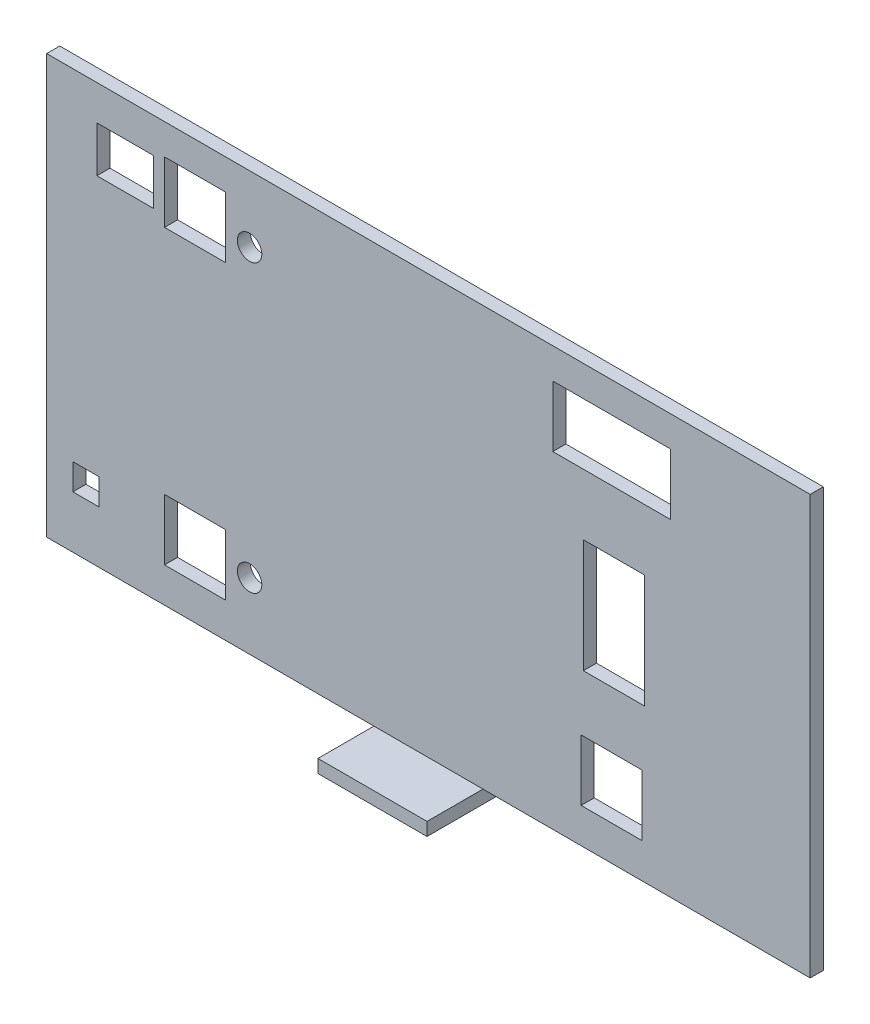
SolidWorks part; units mm, degrees
other "Markup1"
sketch "Sketch6" plane through (-87.5, -48, 0) normal (0, 0, -1) x (-1, 0, 0)
ref_plane "Front Plane" through (0, 0, 0) normal (0, 0, 1) x (1, 0, 0)
ref_plane "Top Plane" through (0, 0, 0) normal (0, 1, 0) x (1, 0, 0)
ref_plane "Right Plane" through (0, 0, 0) normal (1, 0, 0) x (0, 0, -1)
sketch "Sketch2" plane through (0, 0, 0) normal (0, 0, 1) x (1, 0, 0)
  line L1 (87.5, 48) -> (-87.5, 48)
  line L2 (87.5, 48) -> (87.5, -48)
  line L3 (87.5, -48) -> (-87.5, -48)
  line L4 (-87.5, 48) -> (-87.5, -48)
  line L5 (87.5, 48) -> (-87.5, -48) construction
  line L6 (87.5, -48) -> (-87.5, 48) construction
  point P0 (0, 0)
  dimension "D1" = 175
  dimension "D2" = 96
extrude "Boss-Extrude1" add sketch "Sketch2" along normal blind 3
sketch "Sketch3" plane through (0, 0, 0) normal (0, 0, -1) x (-1, 0, 0)
  line L0 (-87.5, 40) -> (-54.5, 40) construction
  line L1 (-87.5, -48) -> (-87.5, 48) construction
  line L2 (-87.5, 48) -> (87.5, 48) construction
  line L3 (-87.5, 28) -> (-29.5, 28) construction
  line L4 (-54.5, 40) -> (-42.5, 40)
  line L5 (-54.5, 40) -> (-54.5, 28)
  line L6 (-54.5, 28) -> (-42.5, 28)
  line L7 (-42.5, 40) -> (-42.5, 28)
  line L8 (87.5, 40) -> (59.5, 40) construction
  line L9 (-29.5, 28) -> (-41.5, 28)
  line L10 (-29.5, 28) -> (-29.5, 40)
  line L11 (-29.5, 40) -> (-41.5, 40)
  line L12 (-41.5, 28) -> (-41.5, 40)
  line L13 (87.5, 48) -> (87.5, -48) construction
  line L15 (59.5, 40) -> (47.5, 40)
  line L16 (59.5, 40) -> (59.5, 28)
  line L17 (59.5, 28) -> (47.5, 28)
  line L18 (47.5, 40) -> (47.5, 28)
  line L19 (63, 40) -> (76, 40)
  line L20 (63, 40) -> (63, 29.5)
  line L21 (63, 29.5) -> (76, 29.5)
  line L22 (76, 40) -> (76, 29.5)
  line L23 (-55.5, 41) -> (-28.5, 41)
  line L24 (-55.5, 41) -> (-55.5, 27)
  line L25 (-55.5, 27) -> (-28.5, 27)
  line L26 (-28.5, 41) -> (-28.5, 27)
  dimension "D1" = 33
  dimension "D2" = 8
  dimension "D3" = 12
  dimension "D4" = 12
  dimension "D5" = 58
  dimension "D6" = 12
  dimension "D7" = 12
  dimension "D8" = 28
  dimension "D9" = 12
  dimension "D10" = 12
  dimension "D11" = 11.5
  dimension "D12" = 13
  dimension "D13" = 10.5
  dimension "D14" = 1
  dimension "D15" = 1
  dimension "D16" = 1
  dimension "D17" = 1
extrude "Cut-Extrude1" cut sketch "Sketch3" against normal blind 10
sketch "Sketch4" plane through (0, 0, 0) normal (0, 0, -1) x (-1, 0, 0)
  line L0 (-87.5, 0) -> (-49.5, 0) construction
  line L1 (-87.5, -48) -> (-87.5, 48) construction
  line L2 (87.5, -48) -> (-87.5, -48) construction
  line L3 (-49.5, 13) -> (-35.5, 13)
  line L4 (-49.5, 13) -> (-49.5, -13)
  line L5 (-49.5, -13) -> (-35.5, -13)
  line L6 (-35.5, 13) -> (-35.5, -13)
  line L7 (-87.5, 48) -> (87.5, 48) construction
  dimension "D1" = 38
  dimension "D2" = 14
  dimension "D3" = 35
  dimension "D4" = 35
  dimension "D5" = 0
extrude "Cut-Extrude2" cut sketch "Sketch4" against normal blind 10
sketch "Sketch5" plane through (0, 0, 0) normal (0, 0, -1) x (-1, 0, 0)
  line L0 (-87.5, -39) -> (-48, -39) construction
  line L1 (-87.5, -48) -> (-87.5, 48) construction
  line L2 (87.5, -48) -> (-87.5, -48) construction
  line L3 (87.5, -39) -> (59.5, -39) construction
  line L4 (-48, -39) -> (-36, -39)
  line L5 (-48, -39) -> (-48, -27)
  line L6 (-48, -27) -> (-36, -27)
  line L7 (-36, -39) -> (-36, -27)
  line L8 (87.5, 48) -> (87.5, -48) construction
  line L9 (87.5, -36) -> (81.5, -36) construction
  line L10 (59.5, -39) -> (47.5, -39)
  line L11 (59.5, -39) -> (59.5, -27)
  line L12 (59.5, -27) -> (47.5, -27)
  line L13 (47.5, -39) -> (47.5, -27)
  line L15 (81.5, -36) -> (75.5, -36)
  line L16 (81.5, -36) -> (81.5, -30)
  line L17 (81.5, -30) -> (75.5, -30)
  line L18 (75.5, -36) -> (75.5, -30)
  dimension "D1" = 39.5
  dimension "D2" = 9
  dimension "D3" = 12
  dimension "D4" = 12
  dimension "D5" = 28
  dimension "D6" = 12
  dimension "D7" = 12
  dimension "D8" = 12
  dimension "D9" = 6
  dimension "D10" = 6
  dimension "D11" = 6
extrude "Cut-Extrude3" cut sketch "Sketch5" against normal blind 10
sketch "Sketch7" plane through (0, 0, 0) normal (0, 0, -1) x (-1, 0, 0)
  line L0 (41, 48) -> (41, 32.8) construction
  line L1 (-87.5, 48) -> (87.5, 48) construction
  line L2 (87.5, 48) -> (87.5, -48) construction
  line L3 (0, 0) -> (87.5, 0) construction
  circle A0 centre (41, 32.8) radius 2.8
  circle A1 centre (41, -32.8) radius 2.8
  dimension "D3" = 5.6
  dimension "D1" = 15.2
  dimension "D2" = 46.5
extrude "Cut-Extrude4" cut sketch "Sketch7" against normal blind 10
sketch "Sketch9" plane through (0, -48, 0) normal (0, -1, 0) x (1, 0, 0)
  line L0 (-87.5, 0) -> (87.5, 0) construction
  line L1 (12.5, 0) -> (-12.5, 0)
  line L2 (12.5, 0) -> (12.5, 15.8299)
  line L3 (12.5, 15.8299) -> (-12.5, 15.8299)
  line L4 (-12.5, 0) -> (-12.5, 15.8299)
  line L5 (-87.5, 3) -> (-87.5, 0) construction
  line L6 (87.5, 3) -> (87.5, 0) construction
  dimension "D1" = 75
  dimension "D2" = 75
extrude "Boss-Extrude2" add sketch "Sketch9" along normal blind 3
sketch "Sketch10" plane through (0, 0, 0) normal (0, 0, -1) x (-1, 0, 0)
  line L1 (-55.5, 41) -> (-28.5, 41)
  line L2 (-55.5, 41) -> (-55.5, 27)
  line L3 (-55.5, 27) -> (-28.5, 27)
  line L4 (-28.5, 41) -> (-28.5, 27)
extrude "Cut-Extrude5" cut sketch "Sketch10" against normal blind 10
sketch "Sketch11" plane through (0, 0, 0) normal (0, 0, -1) x (-1, 0, 0)
  line L0 (59.5, 40) -> (47.5, 40) construction
  line L1 (46.5, 41) -> (60.5, 41)
  line L2 (46.5, 41) -> (46.5, 27)
  line L3 (46.5, 27) -> (60.5, 27)
  line L4 (60.5, 41) -> (60.5, 27)
  line L5 (47.5, 40) -> (47.5, 28) construction
  line L6 (59.5, 28) -> (59.5, 40) construction
  line L7 (47.5, 28) -> (59.5, 28) construction
  dimension "D1" = 1
  dimension "D2" = 1
  dimension "D3" = 1
  dimension "D4" = 1
extrude "Cut-Extrude6" cut sketch "Sketch11" against normal blind 10
sketch "Sketch12" plane through (0, 0, 0) normal (0, 0, -1) x (-1, 0, 0)
  line L0 (47.5, -39) -> (59.5, -39) construction
  line L1 (46.5, -26) -> (60.5, -26)
  line L2 (46.5, -26) -> (46.5, -40)
  line L3 (46.5, -40) -> (60.5, -40)
  line L4 (60.5, -26) -> (60.5, -40)
  line L5 (59.5, -39) -> (59.5, -27) construction
  line L6 (47.5, -27) -> (47.5, -39) construction
  dimension "D1" = 1
  dimension "D2" = 1
  dimension "D3" = 1
  dimension "D4" = 1
extrude "Cut-Extrude7" cut sketch "Sketch12" against normal blind 10
sketch "Sketch13" plane through (0, 0, 0) normal (0, 0, -1) x (-1, 0, 0)
  line L0 (-36, -27) -> (-48, -27) construction
  line L1 (-49, -26) -> (-35, -26)
  line L2 (-49, -26) -> (-49, -40)
  line L3 (-49, -40) -> (-35, -40)
  line L4 (-35, -26) -> (-35, -40)
  line L5 (-48, -39) -> (-36, -39) construction
  line L6 (-36, -39) -> (-36, -27) construction
  line L7 (-48, -27) -> (-48, -39) construction
  point P10 (-36, -33)
  dimension "D1" = 1
  dimension "D2" = 1
  dimension "D3" = 1
  dimension "D4" = 1
extrude "Cut-Extrude8" cut sketch "Sketch13" against normal blind 10
